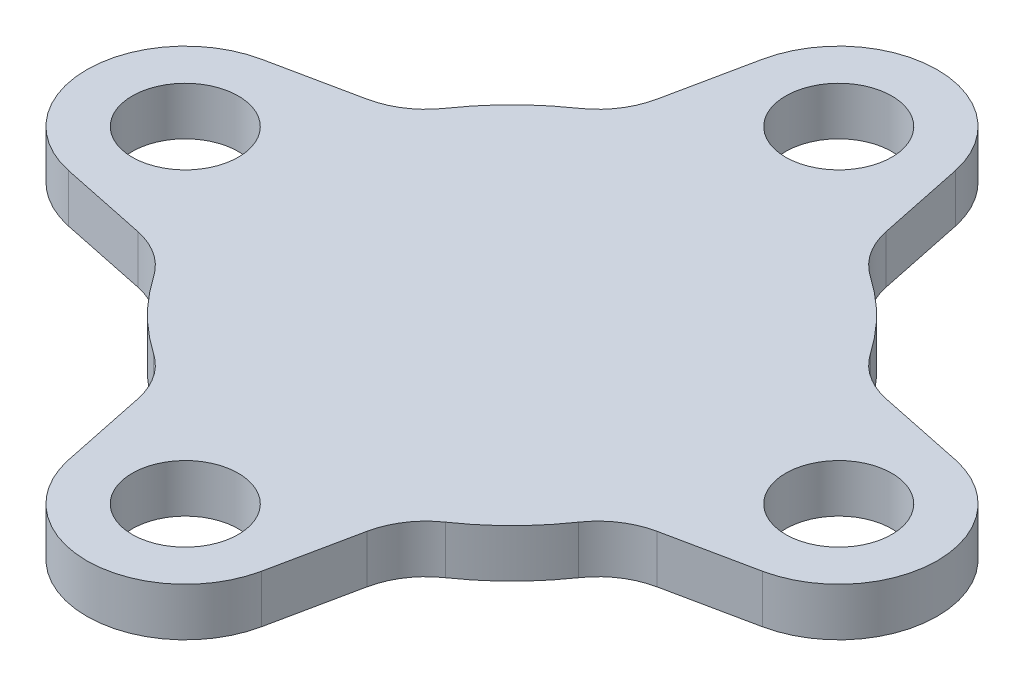
SolidWorks part; units mm, degrees
ref_plane "Front Plane" through (0, 0, 0) normal (0, 0, 1) x (1, 0, 0)
ref_plane "Top Plane" through (0, 0, 0) normal (0, 1, 0) x (1, 0, 0)
ref_plane "Right Plane" through (0, 0, 0) normal (1, 0, 0) x (0, 0, -1)
sketch "Sketch1" plane through (0, 0, 0) normal (0, 1, 0) x (1, 0, 0)
  line L0 (-7.5599, 17.1171) -> (-6.364, 22.8708)
  line L1 (6.364, 22.8708) -> (7.5599, 17.1171)
  line L2 (17.1171, 7.5599) -> (22.8708, 6.364)
  line L3 (22.8708, -6.364) -> (17.1171, -7.5599)
  line L4 (7.5599, -17.1171) -> (6.364, -22.8708)
  line L5 (-6.364, -22.8708) -> (-7.5599, -17.1171)
  line L6 (-17.1171, -7.5599) -> (-22.8708, -6.364)
  line L7 (-22.8708, 6.364) -> (-17.1171, 7.5599)
  arc A1 (-9.6246, 14.0131) -> (-14.0131, 9.6246) centre (0, 0) ccw
  circle A2 centre (0, 21.548) radius 3.5
  circle A3 centre (21.548, 0) radius 3.5
  circle A4 centre (0, -21.548) radius 3.5
  circle A5 centre (-21.548, 0) radius 3.5
  arc A6 (-6.364, 22.8708) -> (6.364, 22.8708) centre (0, 21.548) cw
  arc A7 (7.5599, 17.1171) -> (9.6246, 14.0131) centre (12.4553, 18.1346) ccw
  arc A8 (-7.5599, 17.1171) -> (-9.6246, 14.0131) centre (-12.4553, 18.1346) cw
  arc A9 (22.8708, 6.364) -> (22.8708, -6.364) centre (21.548, 0) cw
  arc A10 (17.1171, 7.5599) -> (14.0131, 9.6246) centre (18.1346, 12.4553) cw
  arc A11 (17.1171, -7.5599) -> (14.0131, -9.6246) centre (18.1346, -12.4553) ccw
  arc A12 (6.364, -22.8708) -> (-6.364, -22.8708) centre (0, -21.548) cw
  arc A13 (7.5599, -17.1171) -> (9.6246, -14.0131) centre (12.4553, -18.1346) cw
  arc A14 (-7.5599, -17.1171) -> (-9.6246, -14.0131) centre (-12.4553, -18.1346) ccw
  arc A15 (-22.8708, -6.364) -> (-22.8708, 6.364) centre (-21.548, 0) cw
  arc A16 (-17.1171, -7.5599) -> (-14.0131, -9.6246) centre (-18.1346, -12.4553) cw
  arc A17 (-17.1171, 7.5599) -> (-14.0131, 9.6246) centre (-18.1346, 12.4553) ccw
  arc A18 (-14.0131, -9.6246) -> (-9.6246, -14.0131) centre (0, 0) ccw
  arc A19 (14.0131, 9.6246) -> (9.6246, 14.0131) centre (0, 0) ccw
  arc A20 (9.6246, -14.0131) -> (14.0131, -9.6246) centre (0, 0) ccw
  point P15 (0, 0)
  point P17 (15.9184, 10.0028)
  point P26 (8, 15)
  point P29 (-8, 15)
  point P30 (0, 0)
  point P53 (0, 0)
  dimension "D1" = 7
  dimension "D4" = 34
  dimension "D5" = 3
  dimension "D7" = 5
  dimension "D8" = 4
  dimension "D2" = 21.548
  dimension "D3" = 4
  dimension "D6" = 16
extrude "Boss-Extrude1" add sketch "Sketch1" along normal blind 3.175
